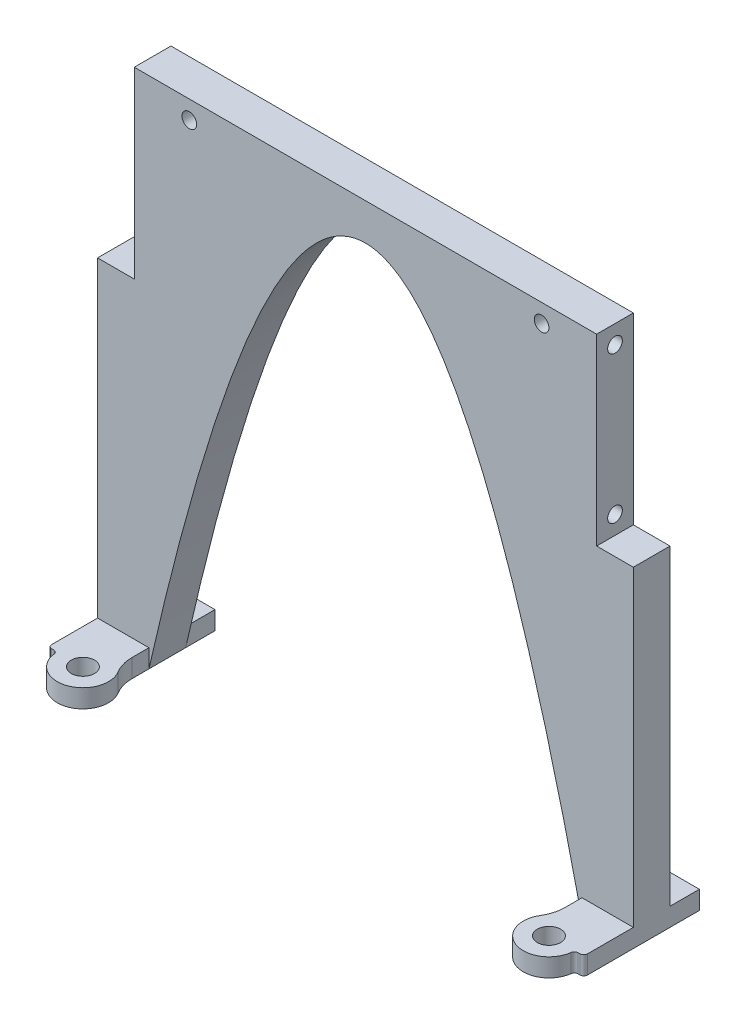
SolidWorks part; units mm, degrees
ref_plane "Front Plane" through (0, 0, 0) normal (0, 0, 1) x (1, 0, 0)
ref_plane "Top Plane" through (0, 0, 0) normal (0, 1, 0) x (1, 0, 0)
ref_plane "Right Plane" through (0, 0, 0) normal (1, 0, 0) x (0, 0, -1)
sketch "Sketch1" plane through (0, 0, 0) normal (0, 0, 1) x (1, 0, 0)
  line L1 (0, 0) -> (146, 0)
  line L2 (0, 0) -> (0, 140)
  line L3 (0, 140) -> (146, 140)
  line L4 (146, 0) -> (146, 140)
  dimension "D1" = 140
  dimension "D2" = 146
extrude "Boss-Extrude1" add sketch "Sketch1" along normal blind 10
sketch "Sketch4" plane through (0, 0, 10) normal (0, 0, 1) x (1, 0, 0)
  line L0 (0, 0) -> (146, 0) construction
  line L1 (73, 0) -> (73, 140) construction
  line L2 (146, 140) -> (0, 140) construction
  line L3 (14, 0) -> (132, 0)
  parabola Q0 (14, 0) -> (132, 0) focus (73, 123.3058) apex (73, 130)
  dimension "D1" = 14
  dimension "D2" = 14
  dimension "D3" = 10
extrude "Cut-Extrude1" cut sketch "Sketch4" against normal blind 10
ref_plane "Plane2" through (73, 0, 0) normal (-1, 0, 0) x (0, 0, 1)
sketch "Sketch8" plane through (0, 140, 0) normal (0, 1, 0) x (1, 0, 0)
  line L0 (0, -10) -> (0, 0) construction
  line L1 (146, -10) -> (146, 0) construction
  circle A0 centre (5, -5) radius 2
  circle A1 centre (141, -5) radius 2
  dimension "D1" = 4
  dimension "D4" = 4
  dimension "D2" = 5
  dimension "D3" = 5
ref_plane "Plane1" through (0, 0, 5) normal (0, 0, 1) x (1, 0, 0)
sketch "Sketch9" plane through (0, 0, 0) normal (-1, 0, 0) x (0, 0, 1)
  line L0 (5, -68.75) -> (5, 68.75) construction
  line L2 (10, 140) -> (0, 140) construction
  circle A0 centre (5, 135) radius 2
  circle A1 centre (5, 95) radius 2
  dimension "D3" = 4
  dimension "D4" = 4
  dimension "D1" = 5
  dimension "D2" = 40
extrude "Cut-Extrude4" cut sketch "Sketch9" against normal blind 20
sketch "Sketch10" plane through (0, 140, 0) normal (0, 1, 0) x (1, 0, 0)
  line L0 (146, -10) -> (0, -10) construction
  line L1 (0, 0) -> (10, 0)
  line L2 (0, 0) -> (0, -10)
  line L3 (0, -10) -> (10, -10)
  line L4 (10, 0) -> (10, -10)
  dimension "D1" = 10
extrude "Cut-Extrude5" cut sketch "Sketch10" against normal blind 50
mirror "Mirror3" about plane through (73, 0, 0) normal (-1, 0, 0) of "Cut-Extrude5", "Cut-Extrude4"
sketch "Sketch12" plane through (0, 0, 0) normal (0, 1, 0) x (1, 0, 0)
  line L0 (0, -10) -> (146, -10) construction
  line L1 (73, -10) -> (73, -59.3881) construction
  line L2 (136.5, -23.5) -> (9.5, -23.5) construction
  line L3 (14, -10) -> (14, -14.6259)
  line L4 (9.5, -23.5) -> (9.5, -10) construction
  line L6 (0, -10) -> (14, -10)
  line L7 (0, -10) -> (0, -22.5)
  line L8 (1, -23.5) -> (1.5627, -23.5)
  circle A0 centre (9.5, -23.5) radius 3.175
  circle A2 centre (9.5, -23.5) radius 7 construction
  arc A3 (2.5549, -24.375) -> (15.4706, -19.846) centre (9.5, -23.5) ccw
  arc A5 (14, -14.6259) -> (15.4706, -19.846) centre (24, -14.6259) ccw
  arc A6 (1.5627, -23.5) -> (2.5549, -24.375) centre (1.5627, -24.5) cw
  arc A7 (0, -22.5) -> (1, -23.5) centre (1, -22.5) ccw
  point P9 (73, -23.5)
  point P20 (5, -18.1381)
  point P22 (14, -18.1381)
  point P26 (2.5, -23.5)
  dimension "D3" = 6.35
  dimension "D4" = 14
  dimension "D8" = 10
  dimension "D5" = 1
  dimension "D1" = 127
  dimension "D2" = 13.5
  dimension "D6" = 4.5
extrude "Boss-Extrude2" add sketch "Sketch12" along normal blind 5
mirror "Mirror4" about plane through (73, 0, 0) normal (-1, 0, 0) of "Boss-Extrude2"
sketch "Sketch14" plane through (0, 0, 0) normal (0, 1, 0) x (1, 0, 0)
  line L1 (0, 0) -> (14, 0)
  line L2 (0, 0) -> (0, 8)
  line L3 (0, 8) -> (14, 8)
  line L4 (14, 0) -> (14, 8)
  dimension "D1" = 8
extrude "Boss-Extrude3" add sketch "Sketch14" along normal blind 5
mirror "Mirror5" about plane through (73, 0, 0) normal (-1, 0, 0) of "Boss-Extrude3"
sketch "Sketch15" plane through (0, 0, 10) normal (0, 0, 1) x (1, 0, 0)
  line L0 (136, 140) -> (10, 140) construction
  line L1 (10, 90) -> (10, 140) construction
  line L2 (136, 90) -> (136, 140) construction
  circle A0 centre (25, 135) radius 2
  circle A1 centre (121, 135) radius 2
  dimension "D5" = 4
  dimension "D6" = 4
  dimension "D1" = 5
  dimension "D2" = 15
  dimension "D3" = 15
  dimension "D4" = 5
extrude "Cut-Extrude6" cut sketch "Sketch15" against normal blind 20
